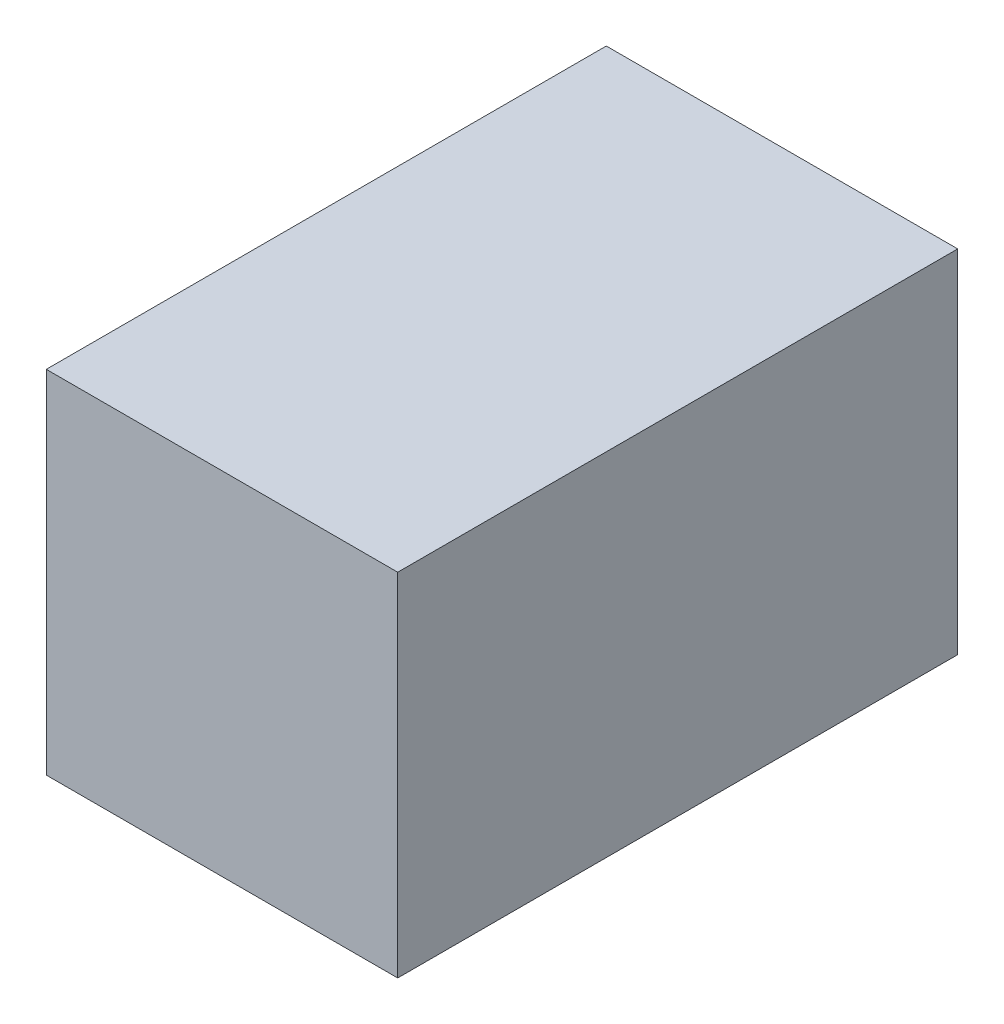
SolidWorks part; units mm, degrees
ref_plane "Piano frontale" through (0, 0, 0) normal (0, 0, 1) x (1, 0, 0)
ref_plane "Piano superiore" through (0, 0, 0) normal (0, 1, 0) x (1, 0, 0)
ref_plane "Piano destro" through (0, 0, 0) normal (1, 0, 0) x (0, 0, -1)
sketch "Schizzo1" plane through (0, 0, 0) normal (0, 0, 1) x (1, 0, 0)
  line L1 (50.2046, 50.2046) -> (-50.2046, 50.2046)
  line L2 (-50.2046, 50.2046) -> (-50.2046, -50.2046)
  line L3 (-50.2046, -50.2046) -> (50.2046, -50.2046)
  line L4 (50.2046, -50.2046) -> (50.2046, 50.2046)
  circle A0 centre (0, 0) radius 50.2046 construction
  dimension "D1" = 71
extrude "Estrusione-Estrusione1" add sketch "Schizzo1" along normal blind 160
